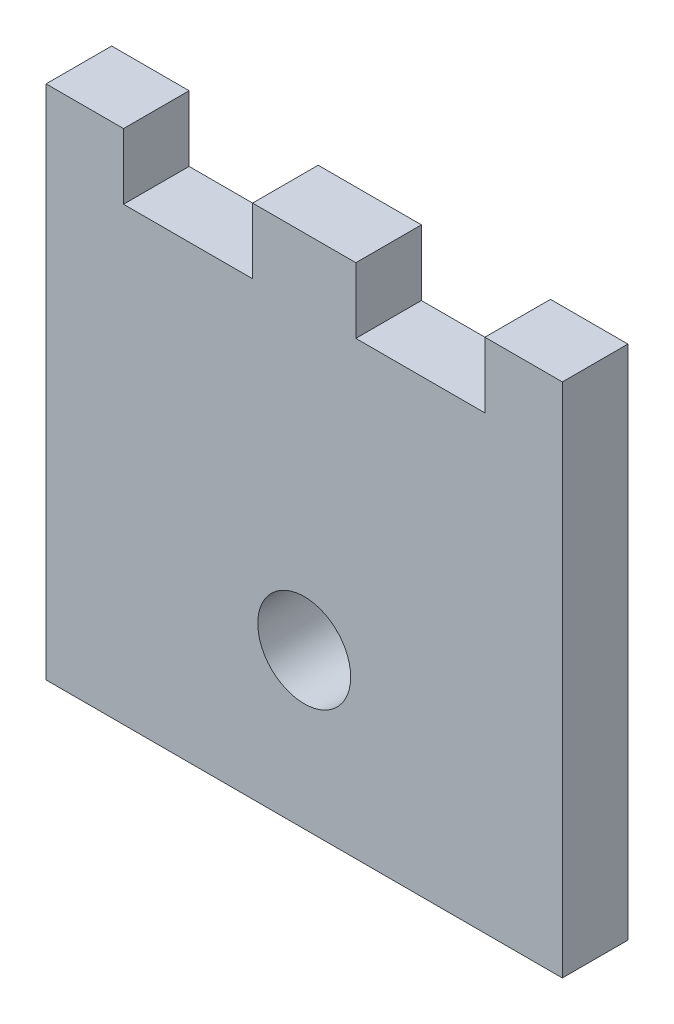
SolidWorks part; units mm, degrees
ref_plane "Front Plane" through (0, 0, 0) normal (0, 0, 1) x (1, 0, 0)
ref_plane "Top Plane" through (0, 0, 0) normal (0, 1, 0) x (1, 0, 0)
ref_plane "Right Plane" through (0, 0, 0) normal (1, 0, 0) x (0, 0, -1)
sketch "Sketch1" plane through (0, 0, 0) normal (0, 0, 1) x (1, 0, 0)
  line L1 (0, 0) -> (50, 0)
  line L2 (0, 0) -> (0, 50)
  line L3 (0, 50) -> (50, 50)
  line L4 (50, 0) -> (50, 50)
  dimension "D1" = 50
  dimension "D2" = 50
extrude "Boss-Extrude1" add sketch "Sketch1" along normal blind 6.35
sketch "Sketch4" plane through (0, 0, 6.35) normal (0, 0, 1) x (1, 0, 0)
  line L0 (50, 50) -> (0, 50) construction
  line L1 (7.5, 50) -> (20, 50)
  line L2 (7.5, 50) -> (7.5, 43.65)
  line L3 (7.5, 43.65) -> (20, 43.65)
  line L4 (20, 50) -> (20, 43.65)
  line L6 (30, 50) -> (42.5, 50)
  line L7 (30, 50) -> (30, 43.65)
  line L8 (30, 43.65) -> (42.5, 43.65)
  line L9 (42.5, 50) -> (42.5, 43.65)
  line L10 (42.5, 46.825) -> (50, 46.825) construction
  line L11 (50, 0) -> (50, 50) construction
  line L12 (0, 46.825) -> (7.5, 46.825) construction
  line L14 (0, 50) -> (0, 0) construction
  line L15 (25, 50) -> (25, 0) construction
  line L16 (0, 0) -> (50, 0) construction
  line L17 (0, 15) -> (50, 15) construction
  line L18 (0, 0) -> (50, 0) construction
  circle A0 centre (25, 15) radius 4.5
  dimension "D1" = 6.35
  dimension "D2" = 12.5
  dimension "D3" = 12.5
  dimension "D4" = 6.35
  dimension "D5" = 7.5
  dimension "D6" = 7.5
  dimension "D7" = 15
extrude "Cut-Extrude1" cut sketch "Sketch4" against normal blind 6.35
